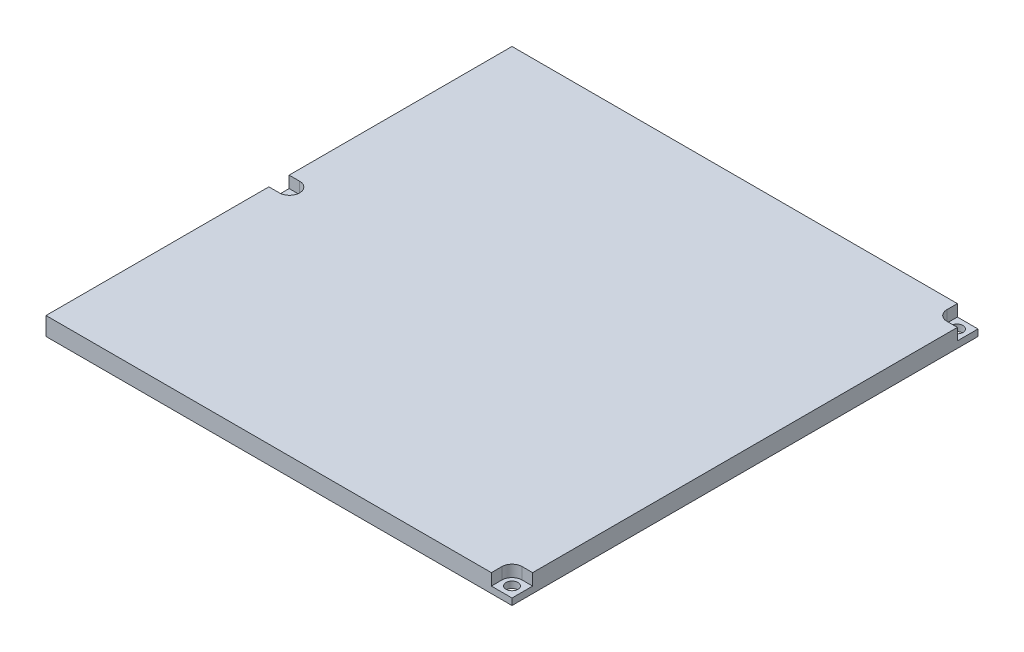
SolidWorks part; units mm, degrees
material "C355.0-T61 Permanent Mold cast (SS)"
ref_plane "Front Plane" through (0, 0, 0) normal (0, 0, 1) x (1, 0, 0)
ref_plane "Top Plane" through (0, 0, 0) normal (0, 1, 0) x (1, 0, 0)
ref_plane "Right Plane" through (0, 0, 0) normal (1, 0, 0) x (0, 0, -1)
sketch "Sketch1" plane through (0, 0, 0) normal (0, 1, 0) x (1, 0, 0)
  line L1 (0, 0) -> (203.2, 0)
  line L2 (0, 0) -> (0, 203.2)
  line L3 (0, 203.2) -> (203.2, 203.2)
  line L4 (203.2, 0) -> (203.2, 203.2)
  dimension "D1" = 203.2
  dimension "D2" = 203.2
extrude "Boss-Extrude1" add sketch "Sketch1" along normal blind 7.9375
sketch "Sketch3" plane through (0, 7.9375, 0) normal (0, 1, 0) x (1, 0, 0)
  line L0 (0, 101.6) -> (203.2, 101.6) construction
  line L4 (0, 203.2) -> (0, 0)
  line L5 (0, 0) -> (203.2, 0)
  line L6 (203.2, 0) -> (203.2, 203.2)
  line L7 (203.2, 203.2) -> (0, 203.2)
  line L8 (0, 203.2) -> (0, 0) construction
  line L9 (0, 0) -> (203.2, 0) construction
  line L10 (203.2, 0) -> (203.2, 203.2) construction
  line L11 (203.2, 203.2) -> (0, 203.2) construction
  circle A0 centre (4.572, 101.6) radius 2.6098
  circle A1 centre (198.628, 198.628) radius 2.6099
  circle A2 centre (198.628, 4.572) radius 2.6099
  dimension "D2" = 5.2197
  dimension "D3" = 4.572
  dimension "D4" = 4.572
  dimension "D5" = 4.572
  dimension "D6" = 4.572
  dimension "D1" = 0
extrude "holes" cut sketch "Sketch3" against normal up to next
sketch "Sketch4" plane through (0, 7.9375, 0) normal (0, 1, 0) x (1, 0, 0)
  line L0 (4.572, 106.0196) -> (0, 106.0196)
  line L1 (0, 203.2) -> (0, 0) construction
  line L2 (4.572, 97.1804) -> (0, 97.1804)
  line L5 (194.2084, 198.628) -> (194.2084, 203.2)
  line L6 (203.2, 203.2) -> (0, 203.2) construction
  line L7 (198.628, 194.2084) -> (203.2, 194.2084)
  line L8 (203.2, 0) -> (203.2, 203.2) construction
  line L9 (194.2084, 4.572) -> (194.2084, 0)
  line L10 (0, 0) -> (203.2, 0) construction
  line L11 (198.628, 8.9916) -> (203.2, 8.9916)
  line L12 (0, 106.0196) -> (0, 97.1804)
  line L13 (194.2084, 0) -> (203.2, 0)
  line L14 (203.2, 0) -> (203.2, 8.9916)
  line L15 (194.2084, 203.2) -> (203.2, 203.2)
  line L16 (203.2, 203.2) -> (203.2, 194.2084)
  circle A0 centre (4.572, 101.6) radius 2.6098 construction
  circle A1 centre (198.628, 198.628) radius 2.6098 construction
  circle A2 centre (198.628, 4.572) radius 2.6099 construction
  circle A3 centre (4.572, 101.6) radius 2.6098
  circle A4 centre (198.628, 198.628) radius 2.6099
  circle A5 centre (198.628, 4.572) radius 2.6099
  arc A6 (4.572, 97.1804) -> (4.572, 106.0196) centre (4.572, 101.6) ccw
  arc A7 (194.2084, 198.628) -> (198.628, 194.2084) centre (198.628, 198.628) ccw
  arc A8 (198.628, 8.9916) -> (194.2084, 4.572) centre (198.628, 4.572) ccw
  dimension "D1" = 8.8392
extrude "counters" cut sketch "Sketch4" against normal blind 5.08
